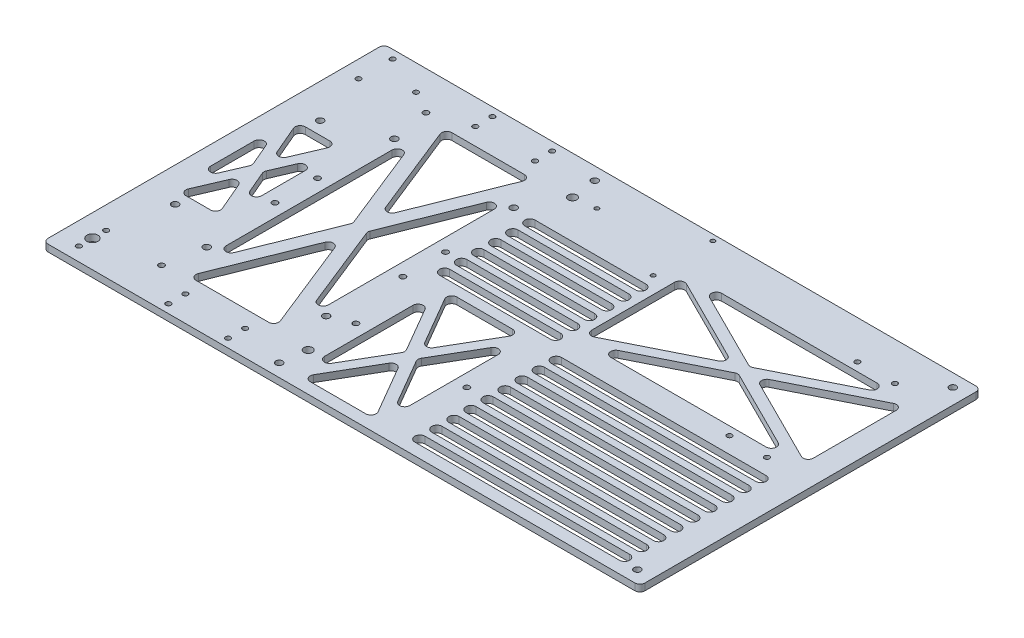
SolidWorks part; units mm, degrees
material "7075-T6 (SN)"
ref_plane "前视基准面" through (0, 0, 0) normal (0, 0, 1) x (1, 0, 0)
ref_plane "上视基准面" through (0, 0, 0) normal (0, 1, 0) x (1, 0, 0)
ref_plane "右视基准面" through (0, 0, 0) normal (1, 0, 0) x (0, 0, -1)
sketch "草图1" plane through (0, 0, 0) normal (0, 1, 0) x (1, 0, 0)
  line L1 (-114, -100) -> (114, -100)
  line L2 (-114, -100) -> (-114, 100)
  line L3 (-114, 100) -> (114, 100)
  line L4 (114, -100) -> (114, 100)
  line L5 (-114, -100) -> (114, 100) construction
  line L6 (-114, 100) -> (114, -100) construction
  point P0 (0, 0)
  dimension "D1" = 228
  dimension "D2" = 200
extrude "凸台-拉伸1" add sketch "草图1" along normal blind 4
sketch "草图2" plane through (0, 4, 0) normal (0, 1, 0) x (1, 0, 0)
  line L1 (-100, -57.5) -> (100, -57.5) construction
  line L2 (-100, -57.5) -> (-100, 57.5) construction
  line L3 (-100, 57.5) -> (100, 57.5) construction
  line L4 (100, -57.5) -> (100, 57.5) construction
  line L5 (-100, -57.5) -> (100, 57.5) construction
  line L6 (-100, 57.5) -> (100, -57.5) construction
  circle A0 centre (-100, 57.5) radius 1.5
  circle A1 centre (100, 57.5) radius 1.5
  circle A2 centre (100, -57.5) radius 1.5
  circle A3 centre (-100, -57.5) radius 1.5
  point P0 (0, 0)
  dimension "D3" = 3
  dimension "D1" = 200
  dimension "D2" = 115
sketch "草图4" plane through (0, 4, 0) normal (0, 1, 0) x (1, 0, 0)
  line L0 (0, 0) -> (-108, 0) construction
  line L1 (-108, -30) -> (-108, 30) construction
  circle A0 centre (-108, 30) radius 2.5
  circle A1 centre (-108, -30) radius 2.5
  point P6 (-108, 0)
  dimension "D2" = 5
  dimension "D1" = 108
  dimension "D3" = 60
sketch "草图5" plane through (0, 0, 0) normal (0, -1, 0) x (-1, 0, 0)
  line L1 (-10, -42) -> (-85, -42) construction
  line L2 (-10, -42) -> (-10, -20) construction
  line L3 (-10, -20) -> (-85, -20) construction
  line L4 (-85, -42) -> (-85, -20) construction
  circle A0 centre (-10, -42) radius 1.5
  circle A1 centre (-10, -20) radius 1.5
  circle A2 centre (-85, -42) radius 1.5
  circle A3 centre (-85, -20) radius 1.5
  dimension "D3" = 3
  dimension "D1" = 75
  dimension "D2" = 22
  dimension "D4" = 10
  dimension "D5" = 20
sketch "草图7" plane through (-114, 0, 0) normal (-1, 0, 0) x (0, 0, 1)
  line L4 (-100, 0) -> (100, 0)
  line L5 (100, 0) -> (100, 4)
  line L6 (100, 4) -> (-100, 4)
  line L7 (-100, 4) -> (-100, 0)
  line L8 (-100, 0) -> (100, 0)
  line L9 (100, 0) -> (100, 4)
  line L10 (100, 4) -> (-100, 4)
  line L11 (-100, 4) -> (-100, 0)
  dimension "D1" = 0
extrude "凸台-拉伸2" add sketch "草图7" along normal blind 122
sketch "草图10" plane through (0, 4, 0) normal (0, 1, 0) x (1, 0, 0)
  line L1 (-105, 92.5) -> (105, 92.5) construction
  line L2 (-105, 92.5) -> (-105, -92.5) construction
  line L3 (-105, -92.5) -> (105, -92.5) construction
  line L4 (105, 92.5) -> (105, -92.5) construction
  line L5 (-105, 92.5) -> (105, -92.5) construction
  line L6 (-105, -92.5) -> (105, 92.5) construction
  circle A0 centre (-105, 92.5) radius 2
  circle A1 centre (-105, -92.5) radius 2
  circle A2 centre (105, -92.5) radius 2
  circle A3 centre (105, 92.5) radius 2
  point P0 (0, 0)
  dimension "D3" = 4
  dimension "D1" = 185
  dimension "D2" = 210
extrude "切除-拉伸5" cut sketch "草图10" against normal through all
sketch "草图17" plane through (0, 4, 0) normal (0, 1, 0) x (1, 0, 0)
  line L0 (-236, 0) -> (-216, 0) construction
  line L2 (-216, -42.5) -> (-216, 42.5) construction
  line L4 (-236, -100) -> (-236, 100) construction
  line L5 (-236, 100) -> (-236, -100) construction
  circle A0 centre (-216, 42.5) radius 2
  circle A1 centre (-216, -42.5) radius 2
  point P8 (-216, 0)
  dimension "D3" = 4
  dimension "D1" = 85
  dimension "D2" = 20
  dimension "D4" = 0
extrude "切除-拉伸9" cut sketch "草图17" against normal through all
sketch "草图18" plane through (0, 4, 0) normal (0, 1, 0) x (1, 0, 0)
  line L0 (-236, 85) -> (-226, 85) construction
  line L1 (-236, -100) -> (-236, 100) construction
  line L2 (-226, 95) -> (-226, 75) construction
  line L3 (-226, 85) -> (-202.3, 85) construction
  line L5 (-236, 100) -> (-236, -100) construction
  line L6 (114, 100) -> (-236, 100) construction
  circle A0 centre (-226, 95) radius 1.5
  circle A1 centre (-226, 75) radius 1.5
  circle A2 centre (-202.3, 85) radius 1.5
  point P7 (-226, 85)
  dimension "D2" = 3
  dimension "D1" = 20
  dimension "D3" = 23.7
  dimension "D4" = 10
  dimension "D5" = 15
extrude "切除-拉伸11" cut sketch "草图18" against normal through all
sketch "草图19" plane through (0, 0, 0) normal (0, -1, 0) x (1, 0, 0)
  line L0 (-236, 84) -> (-223, 84) construction
  line L1 (-236, -100) -> (-236, 100) construction
  line L2 (-223, 92) -> (-223, 76) construction
  line L4 (-236, 100) -> (114, 100) construction
  circle A0 centre (-223, 92) radius 1.5
  circle A1 centre (-223, 76) radius 1.5
  circle A2 centre (-223, 84) radius 3.2
  point P6 (-223, 84)
  dimension "D4" = 3
  dimension "D5" = 6.4
  dimension "D1" = 16
  dimension "D2" = 13
  dimension "D3" = 8
extrude "切除-拉伸12" cut sketch "草图19" against normal through all
sketch "草图23" plane through (0, 0, 0) normal (0, -1, 0) x (1, 0, 0)
  line L0 (0, 0) -> (-150, 0) construction
  line L2 (-115, -55) -> (-185, -55) construction
  line L3 (-115, -55) -> (-115, 55) construction
  line L4 (-115, 55) -> (-185, 55) construction
  line L5 (-185, -55) -> (-185, 55) construction
  line L6 (-115, -55) -> (-185, 55) construction
  line L7 (-115, 55) -> (-185, -55) construction
  circle A0 centre (-185, -55) radius 2
  circle A1 centre (-115, -55) radius 2
  circle A2 centre (-185, 55) radius 2
  circle A3 centre (-115, 55) radius 2
  dimension "D4" = 4
  dimension "D1" = 110
  dimension "D2" = 70
  dimension "D3" = 150
extrude "切除-拉伸15" cut sketch "草图23" against normal through all
sketch "草图25" plane through (0, 0, 0) normal (0, -1, 0) x (1, 0, 0)
  line L0 (-70, 60) -> (0, 60) construction
  line L1 (-95, 42.5) -> (-45, 42.5) construction
  line L2 (-95, 42.5) -> (-95, 77.5) construction
  line L3 (-95, 77.5) -> (-45, 77.5) construction
  line L4 (-45, 42.5) -> (-45, 77.5) construction
  line L5 (-95, 42.5) -> (-45, 77.5) construction
  line L6 (-95, 77.5) -> (-45, 42.5) construction
  line L7 (0, 0) -> (0, 60) construction
  circle A3 centre (-45, 77.5) radius 1.5
  circle A4 centre (-45, 42.5) radius 1.5
  circle A5 centre (-95, 60) radius 1.5
  point P0 (-70, 60)
  dimension "D4" = 3
  dimension "D1" = 70
  dimension "D2" = 35
  dimension "D3" = 50
  dimension "D5" = 60
hole_wizard "M3 螺纹孔2" [suppressed] positions "3D草图2" profile "草图27" tap size "M3" standard "ISO"
sketch3d "3D草图2"
  point P0 (-95, 0, 60)
  point P3 (-45, 0, 77.5)
  point P6 (-45, 0, 42.5)
sketch "草图27" plane through (-95, 0, 60) normal (1, 0, 0) x (0, 0, -1)
  line L0 (0, 0) -> (0, 3)
  line L1 (0, 3) -> (1.25, 3)
  line L2 (1.25, 3) -> (1.25, 0)
  line L5 (1.25, 0) -> (0, 0)
  line L11 (0, -6.35) -> (0, 107.95) construction
  dimension "通孔螺纹孔钻头直径" = 2.5
  dimension "通孔螺纹孔钻头深度" = 3
cosmetic thread "孔螺蚊线4" [suppressed] parameters "D2"=3
cosmetic thread "孔螺蚊线5" [suppressed] parameters "D2"=3
cosmetic thread "孔螺蚊线6" [suppressed] parameters "D2"=3
sketch "草图28" plane through (0, 0, 0) normal (0, -1, 0) x (1, 0, 0)
  line L0 (-60, 0) -> (0, 0) construction
  line L2 (-115, -35) -> (-5, -35) construction
  line L3 (-115, -35) -> (-115, 35) construction
  line L4 (-115, 35) -> (-5, 35) construction
  line L5 (-5, -35) -> (-5, 35) construction
  line L6 (-115, -35) -> (-5, 35) construction
  line L7 (-115, 35) -> (-5, -35) construction
  circle A0 centre (-115, 35) radius 2
  circle A1 centre (-5, 35) radius 2
  circle A2 centre (-115, -35) radius 2
  circle A3 centre (-5, -35) radius 2
  dimension "D4" = 4
  dimension "D1" = 60
  dimension "D2" = 110
  dimension "D3" = 70
extrude "切除-拉伸16" [suppressed] cut sketch "草图28" against normal through all
sketch "草图29" [suppressed] plane through (0, 0, 0) normal (0, -1, 0) x (-1, 0, 0)
  line L0 (115, -35) -> (5, 35) construction
  line L1 (92.5, 0) -> (27.5, 0) construction
  circle A0 centre (92.5, 0) radius 2
  circle A1 centre (27.5, 0) radius 2
  point P8 (60, 0)
  dimension "D2" = 4
  dimension "D1" = 65
extrude "切除-拉伸17" [suppressed] cut sketch "草图29" against normal through all
sketch "草图30" plane through (0, 0, 0) normal (0, -1, 0) x (1, 0, 0)
  line L1 (86, -2.5) -> (64, -2.5) construction
  line L2 (86, -2.5) -> (86, -77.5) construction
  line L3 (86, -77.5) -> (64, -77.5) construction
  line L4 (64, -2.5) -> (64, -77.5) construction
  line L5 (86, -2.5) -> (64, -77.5) construction
  line L6 (86, -77.5) -> (64, -2.5) construction
  circle A0 centre (86, -77.5) radius 1.5
  circle A1 centre (64, -77.5) radius 1.5
  circle A2 centre (64, -2.5) radius 1.5
  circle A3 centre (86, -2.5) radius 1.5
  point P0 (75, -40)
  dimension "D5" = 3
  dimension "D1" = 75
  dimension "D2" = 22
  dimension "D3" = 75
  dimension "D4" = 40
extrude "切除-拉伸18" cut sketch "草图30" against normal through all
sketch "草图33" plane through (0, 4, 0) normal (0, 1, 0) x (1, 0, 0)
  line L0 (-236, 77.5) -> (-189, 77.5) construction
  line L1 (-236, -100) -> (-236, 100) construction
  line L2 (-189, 77.5) -> (-189, 100) construction
  line L3 (114, 100) -> (-236, 100) construction
  dimension "D1" = 47
  dimension "D2" = 22.5
hole_wizard "M4 螺纹孔3" positions "3D草图3" profile "草图34" tap size "M4" standard "ISO" end condition up to next
sketch3d "3D草图3"
  point P0 (-189, 4, -77.5)
sketch "草图34" plane through (-189, 4, -77.5) normal (1, 0, 0) x (0, 0, 1)
  line L0 (0, 0) -> (0, 4)
  line L1 (0, 4) -> (1.65, 4)
  line L2 (1.65, 4) -> (1.65, 0)
  line L5 (1.65, 0) -> (0, 0)
  line L11 (0, -6.35) -> (0, 107.95) construction
  dimension "通孔螺纹孔钻头直径" = 3.3
  dimension "通孔螺纹孔钻头深度" = 4
cosmetic thread "孔螺蚊线7" parameters "D2"=4
mirror "镜向1" about plane through (0, 0, 0) normal (0, 0, 1) of "M4 螺纹孔3"
cosmetic thread "孔螺蚊线8" parameters "D2"=4
sketch "草图35" plane through (0, 0, 0) normal (0, -1, 0) x (1, 0, 0)
  line L0 (-150, 0) -> (0, 0) construction
  line L1 (-167.5, 95) -> (-132.5, 95) construction
  line L2 (-167.5, 95) -> (-167.5, -95) construction
  line L3 (-167.5, -95) -> (-132.5, -95) construction
  line L4 (-132.5, 95) -> (-132.5, -95) construction
  line L5 (-167.5, 95) -> (-132.5, -95) construction
  line L6 (-167.5, -95) -> (-132.5, 95) construction
  line L8 (-167.5, 85) -> (-132.5, 85) construction
  line L9 (-167.5, 85) -> (-167.5, -85) construction
  line L10 (-167.5, -85) -> (-132.5, -85) construction
  line L11 (-132.5, 85) -> (-132.5, -85) construction
  line L12 (-167.5, 85) -> (-132.5, -85) construction
  line L13 (-167.5, -85) -> (-132.5, 85) construction
  circle A0 centre (-167.5, 95) radius 1.5
  circle A1 centre (-132.5, 95) radius 1.5
  circle A2 centre (-167.5, -95) radius 1.5
  circle A3 centre (-132.5, -95) radius 1.5
  circle A4 centre (-132.5, 85) radius 1.5
  circle A5 centre (-167.5, 85) radius 1.5
  circle A6 centre (-132.5, -85) radius 1.5
  circle A7 centre (-167.5, -85) radius 1.5
  point P0 (-150, 0)
  dimension "D4" = 3
  dimension "D1" = 150
  dimension "D2" = 190
  dimension "D3" = 35
  dimension "D5" = 10
extrude "切除-拉伸19" cut sketch "草图35" against normal through all
sketch "草图37" plane through (0, 0, 0) normal (0, -1, 0) x (-1, 0, 0)
  line L0 (150, 0) -> (0, 0) construction
  line L1 (187.5, 12.5) -> (112.5, 12.5) construction
  line L2 (187.5, 12.5) -> (187.5, -12.5) construction
  line L3 (187.5, -12.5) -> (112.5, -12.5) construction
  line L4 (112.5, 12.5) -> (112.5, -12.5) construction
  line L5 (187.5, 12.5) -> (112.5, -12.5) construction
  line L6 (187.5, -12.5) -> (112.5, 12.5) construction
  point P0 (150, 0)
  dimension "D1" = 25
  dimension "D2" = 75
  dimension "D3" = 150
hole_wizard "M4 螺纹孔1" positions "3D草图4" profile "草图38" tap size "M4" standard "ISO" end condition up to next
sketch3d "3D草图4"
  point P0 (-112.5, 0, -12.5)
  point P3 (-112.5, 0, 12.5)
  point P6 (-187.5, 0, 12.5)
  point P9 (-187.5, 0, -12.5)
sketch "草图38" plane through (-112.5, 0, -12.5) normal (1, 0, 0) x (0, 0, -1)
  line L0 (0, 0) -> (0, 4)
  line L1 (0, 4) -> (1.65, 4)
  line L2 (1.65, 4) -> (1.65, 0)
  line L5 (1.65, 0) -> (0, 0)
  line L11 (0, -6.35) -> (0, 107.95) construction
  dimension "通孔螺纹孔钻头直径" = 3.3
  dimension "通孔螺纹孔钻头深度" = 4
cosmetic thread "孔螺蚊线9" parameters "D2"=4
cosmetic thread "孔螺蚊线10" parameters "D2"=4
cosmetic thread "孔螺蚊线11" parameters "D2"=4
cosmetic thread "孔螺蚊线12" parameters "D2"=4
sketch "草图39" plane through (0, 0, 0) normal (0, -1, 0) x (-1, 0, 0)
  line L0 (0, 0) -> (-75, 0) construction
  line L1 (-75, 0) -> (-75, -20) construction
  line L2 (-86, 77.5) -> (-64, 77.5) construction
  line L3 (-75, 77.5) -> (-75, 0) construction
  line L4 (-25.5676, -57.7053) -> (-120.5676, 22.2947)
  line L5 (-27.5, -60) -> (-122.5, -60)
  line L6 (-27.5, -60) -> (-27.5, 20)
  line L7 (-27.5, 20) -> (-122.5, 20)
  line L8 (-122.5, -60) -> (-122.5, 20)
  line L9 (-27.5, -60) -> (-122.5, 20) construction
  line L10 (-27.5, 20) -> (-122.5, -60) construction
  line L11 (-29.4324, 22.2947) -> (-124.4324, -57.7053)
  line L12 (-29.4324, -62.2947) -> (-124.4324, 17.7053)
  line L13 (-25.5676, 17.7053) -> (-120.5676, -62.2947)
  dimension "D1" = 20
  dimension "D2" = 80
  dimension "D3" = 95
  dimension "D4" = 3
  dimension "D5" = 3
extrude "切除-拉伸20" [suppressed] cut sketch "草图39" against normal blind 10 contours L12 L13 L5 | L6 L13 L4 | L11 L7 L4 | L11 L12 L8
sketch "草图40" plane through (0, 0, 0) normal (0, -1, 0) x (-1, 0, 0)
  line L0 (0, 0) -> (-50, 0) construction
  line L1 (-10, -60) -> (-90, -60)
  line L2 (-10, -60) -> (-10, -10)
  line L3 (-10, -10) -> (-90, -10)
  line L4 (-90, -60) -> (-90, -10)
  line L5 (-10, -60) -> (-90, -10) construction
  line L6 (-10, -10) -> (-90, -60) construction
  line L7 (-50, 0) -> (-50, -35) construction
  line L8 (236, -100) -> (-114, -100) construction
  line L9 (-8.41, -57.456) -> (-88.41, -7.456)
  line L10 (-11.59, -7.456) -> (-91.59, -57.456)
  line L11 (-11.59, -62.544) -> (-91.59, -12.544)
  line L12 (-8.41, -12.544) -> (-88.41, -62.544)
  point P0 (-50, -35)
  dimension "D1" = 50
  dimension "D2" = 80
  dimension "D3" = 50
  dimension "D4" = 40
  dimension "D5" = 3
  dimension "D6" = 3
extrude "切除-拉伸21" [suppressed] cut sketch "草图40" against normal blind 10 contours L2 L12 L9 | L11 L12 L1 | L10 L11 L4 | L10 L3 L9
mirror "镜向2" [suppressed] about plane through (0, 0, 0) normal (0, 0, 1)
sketch "草图43" plane through (0, 0, 0) normal (0, -1, 0) x (-1, 0, 0)
  line L0 (185, -55) -> (115, 55) construction
  line L1 (183.7139, -73.5144) -> (123.7139, 76.4856)
  line L2 (180, 75) -> (120, 75)
  line L3 (180, 75) -> (180, -75)
  line L4 (180, -75) -> (120, -75)
  line L5 (120, 75) -> (120, -75)
  line L6 (180, 75) -> (120, -75) construction
  line L7 (180, -75) -> (120, 75) construction
  line L8 (176.2861, 76.4856) -> (116.2861, -73.5144)
  line L9 (176.2861, -76.4856) -> (116.2861, 73.5144)
  line L10 (183.7139, 73.5144) -> (123.7139, -76.4856)
  point P4 (150, 0)
  dimension "D1" = 60
  dimension "D2" = 150
  dimension "D3" = 4
  dimension "D4" = 4
extrude "切除-拉伸22" cut sketch "草图43" against normal blind 10 contours L9 L10 L4 | L8 L9 L5 | L8 L2 L1 | L3 L10 L1
fillet "圆角1" [suppressed] radius 3
sketch "草图44" [suppressed] plane through (0, 0, 0) normal (0, -1, 0) x (1, 0, 0)
  line L0 (-97.5, -29) -> (-22.5, -51) construction
  line L1 (-60, -40) -> (-60, -58) construction
  line L2 (-102.8426, -20) -> (-17.1574, -20) construction
  line L3 (-35, -88) -> (-85, -88)
  line L4 (-35, -88) -> (-35, -28)
  line L5 (-35, -28) -> (-85, -28)
  line L6 (-85, -88) -> (-85, -28)
  line L7 (-35, -88) -> (-85, -28) construction
  line L8 (-35, -28) -> (-85, -88) construction
  line L10 (-32.6953, -86.0794) -> (-82.6953, -26.0794)
  line L11 (-37.3047, -26.0794) -> (-87.3047, -86.0794)
  line L12 (-37.3047, -89.9206) -> (-87.3047, -29.9206)
  line L13 (-32.6953, -29.9206) -> (-82.6953, -89.9206)
  dimension "D1" = 50
  dimension "D2" = 60
  dimension "D3" = 8
  dimension "D4" = 3
  dimension "D5" = 3
extrude "切除-拉伸23" [suppressed] cut sketch "草图44" against normal blind 10 contours L11 L5 L10 | L4 L13 L10 | L12 L13 L3 | L11 L12 L6
sketch "草图45" plane through (0, 0, 0) normal (0, -1, 0) x (1, 0, 0)
  line L0 (0, 0) -> (-70, 0) construction
  line L1 (-70, 50) -> (-70, 0) construction
  line L2 (-37.5, 50) -> (-102.5, 50) construction
  circle A0 centre (-37.5, 50) radius 2
  circle A1 centre (-102.5, 50) radius 2
  point P6 (-70, 50)
  dimension "D4" = 4
  dimension "D1" = 65
  dimension "D2" = 50
  dimension "D3" = 70
hole_wizard "M4 螺纹孔2" positions "3D草图6" profile "草图47" tap size "M4" standard "ISO" end condition up to next
sketch3d "3D草图6"
  point P0 (-37.5, 0, 50)
  point P3 (-102.5, 0, 50)
sketch "草图47" plane through (-37.5, 0, 50) normal (1, 0, 0) x (0, 0, -1)
  line L0 (0, 0) -> (0, 4)
  line L1 (0, 4) -> (1.65, 4)
  line L2 (1.65, 4) -> (1.65, 0)
  line L5 (1.65, 0) -> (0, 0)
  line L11 (0, -6.35) -> (0, 107.95) construction
  dimension "通孔螺纹孔钻头直径" = 3.3
  dimension "通孔螺纹孔钻头深度" = 4
cosmetic thread "孔螺蚊线13" parameters "D2"=4
cosmetic thread "孔螺蚊线14" parameters "D2"=4
sketch "草图48" plane through (0, 0, 0) normal (0, -1, 0) x (1, 0, 0)
  line L0 (0, 0) -> (-65, 0) construction
  line L1 (-65, 0) -> (-65, -79) construction
  line L2 (-65, -79) -> (-90.25, -79) construction
  line L3 (-90.25, -61.5) -> (-39.75, -61.5) construction
  line L4 (-90.25, -61.5) -> (-90.25, -96.5) construction
  line L5 (-90.25, -96.5) -> (-39.75, -96.5) construction
  line L6 (-39.75, -61.5) -> (-39.75, -96.5) construction
  line L7 (-90.25, -61.5) -> (-39.75, -96.5) construction
  line L8 (-90.25, -96.5) -> (-39.75, -61.5) construction
  circle A0 centre (-39.75, -61.5) radius 1.5
  circle A1 centre (-39.75, -96.5) radius 1.5
  circle A2 centre (-90.25, -79) radius 1.5
  dimension "D5" = 3
  dimension "D1" = 50.5
  dimension "D2" = 35
  dimension "D3" = 65
  dimension "D4" = 79
hole_wizard "M3 螺纹孔4" positions "3D草图7" profile "草图49" tap size "M3" standard "ISO" end condition up to next
sketch3d "3D草图7"
  point P0 (-90.25, 0, -79)
  point P3 (-39.75, 0, -61.5)
  point P6 (-39.75, 0, -96.5)
sketch "草图49" plane through (-90.25, 0, -79) normal (1, 0, 0) x (0, 0, -1)
  line L0 (0, 0) -> (0, 4)
  line L1 (0, 4) -> (1.25, 4)
  line L2 (1.25, 4) -> (1.25, 0)
  line L5 (1.25, 0) -> (0, 0)
  line L11 (0, -6.35) -> (0, 107.95) construction
  dimension "通孔螺纹孔钻头直径" = 2.5
  dimension "通孔螺纹孔钻头深度" = 4
cosmetic thread "孔螺蚊线15" parameters "D2"=3
cosmetic thread "孔螺蚊线16" parameters "D2"=3
cosmetic thread "孔螺蚊线17" parameters "D2"=3
sketch "草图51" plane through (0, 0, 0) normal (0, -1, 0) x (-1, 0, 0)
  line L0 (0, 0) -> (-35, 0) construction
  line L1 (-35, 0) -> (-35, -30) construction
  line L6 (236, -100) -> (-114, -100) construction
  line L11 (30, -80) -> (-100, -80)
  line L12 (30, -80) -> (30, 20)
  line L13 (30, 20) -> (-100, 20)
  line L14 (-100, -80) -> (-100, 20)
  line L15 (30, -80) -> (-100, 20) construction
  line L16 (30, 20) -> (-100, -80) construction
  line L17 (31.8291, -77.6221) -> (-98.1709, 22.3779)
  line L18 (28.1709, 22.3779) -> (-101.8291, -77.6221)
  line L19 (28.1709, -82.3779) -> (-101.8291, 17.6221)
  line L20 (31.8291, 17.6221) -> (-98.1709, -82.3779)
  dimension "D1" = 130
  dimension "D2" = 100
  dimension "D3" = 20
  dimension "D4" = 35
  dimension "D5" = 3
  dimension "D6" = 3
extrude "切除-拉伸25" [suppressed] cut sketch "草图51" against normal blind 10 contours L19 L20 L11 | L18 L19 L14 | L18 L13 L17 | L12 L20 L17
sketch "草图52" plane through (0, 0, 0) normal (0, -1, 0) x (1, 0, 0)
  line L0 (-39.75, -61.5) -> (-39.75, -96.5) construction
  line L1 (-90.25, -79) -> (-39.75, -79) construction
  line L2 (-236, 100) -> (114, 100) construction
  line L3 (-80, -238) -> (-50, -238)
  line L4 (-80, -238) -> (-80, 80)
  line L5 (-80, 80) -> (-50, 80)
  line L6 (-50, -238) -> (-50, 80)
  line L7 (-80, -238) -> (-50, 80) construction
  line L8 (-80, 80) -> (-50, -238) construction
  line L9 (-82.9867, 79.7182) -> (-52.9867, -238.2818)
  line L10 (-77.0133, -238.2818) -> (-47.0133, 79.7182)
  line L11 (-77.0133, 80.2818) -> (-47.0133, -237.7182)
  line L12 (-82.9867, -237.7182) -> (-52.9867, 80.2818)
  point P7 (-65, -79)
  point P14 (-65, -79)
  dimension "D1" = 20
  dimension "D2" = 30
  dimension "D3" = 3
  dimension "D4" = 3
extrude "切除-拉伸26" [suppressed] cut sketch "草图52" against normal blind 10 contours L11 L12 L5 | L10 L11 L6 | L10 L3 L9 | L4 L12 L9
sketch "草图53" plane through (0, 0, 0) normal (0, -1, 0) x (-1, 0, 0)
  line L0 (-64, 2.5) -> (-86, 77.5) construction
  line L1 (-75, 40) -> (-75, 60) construction
  line L2 (-47.6953, 31.9206) -> (-97.6953, 91.9206)
  line L3 (-50, 30) -> (-100, 30)
  line L4 (-50, 30) -> (-50, 90)
  line L5 (-50, 90) -> (-100, 90)
  line L6 (-100, 30) -> (-100, 90)
  line L7 (-50, 30) -> (-100, 90) construction
  line L8 (-50, 90) -> (-100, 30) construction
  line L9 (-52.3047, 91.9206) -> (-102.3047, 31.9206)
  line L10 (-52.3047, 28.0794) -> (-102.3047, 88.0794)
  line L11 (-47.6953, 88.0794) -> (-97.6953, 28.0794)
  dimension "D1" = 50
  dimension "D2" = 60
  dimension "D3" = 20
  dimension "D4" = 3
  dimension "D5" = 3
extrude "切除-拉伸27" [suppressed] cut sketch "草图53" against normal blind 10 contours L9 L5 L2 | L4 L11 L2 | L10 L11 L3 | L9 L10 L6
sketch "草图54" plane through (114, 0, 0) normal (1, 0, 0) x (0, 0, -1)
  line L4 (-100, 0) -> (100, 0)
  line L5 (100, 0) -> (100, 4)
  line L6 (100, 4) -> (-100, 4)
  line L7 (-100, 4) -> (-100, 0)
  line L8 (-100, 0) -> (100, 0)
  line L9 (100, 0) -> (100, 4)
  line L10 (100, 4) -> (-100, 4)
  line L11 (-100, 4) -> (-100, 0)
  dimension "D1" = 0
extrude "凸台-拉伸3" [suppressed] add sketch "草图54" along normal blind 10
sketch "草图56" [suppressed] plane through (0, 3, 0) normal (0, 1, 0) x (1, 0, 0)
  line L0 (0, 0) -> (119, 0) construction
  line L1 (119, 40) -> (119, -40) construction
  line L2 (124, 100) -> (124, -100) construction
  circle A0 centre (119, 40) radius 2.5
  circle A1 centre (119, -40) radius 2.5
  point P6 (119, 0)
  dimension "D3" = 5
  dimension "D1" = 5
  dimension "D2" = 80
extrude "切除-拉伸28" [suppressed] cut sketch "草图56" against normal through all
sketch "草图57" plane through (0, 0, 0) normal (0, -1, 0) x (-1, 0, 0)
  line L0 (39.75, 96.5) -> (39.75, 61.5) construction
  line L1 (90.25, 79) -> (39.75, 79) construction
  line L3 (40, 106.5) -> (90, 106.5) construction
  line L4 (40, 106.5) -> (40, 51.5) construction
  line L5 (40, 51.5) -> (90, 51.5) construction
  line L6 (90, 106.5) -> (90, 51.5) construction
  line L7 (40, 106.5) -> (90, 51.5) construction
  line L8 (40, 51.5) -> (90, 106.5) construction
  circle A0 centre (40, 106.5) radius 1.65
  circle A1 centre (90, 106.5) radius 1.65
  circle A2 centre (90, 51.5) radius 1.65
  circle A3 centre (40, 51.5) radius 1.65
  point P7 (65, 79)
  dimension "D3" = 3.3
  dimension "D1" = 55
  dimension "D2" = 50
extrude "切除-拉伸29" [suppressed] cut sketch "草图57" against normal blind 10
sketch "草图58" plane through (0, 0, 0) normal (0, -1, 0) x (-1, 0, 0)
  line L1 (-114, -100) -> (103, -100) construction
  line L2 (-114, -100) -> (-114, -77.5) construction
  line L3 (-114, -77.5) -> (103, -77.5) construction
  line L4 (103, -100) -> (103, -77.5) construction
  circle A0 centre (103, -77.5) radius 2.5
  dimension "D3" = 5
  dimension "D1" = 22.5
  dimension "D2" = 217
extrude "切除-拉伸30" cut sketch "草图58" against normal through all
mirror "镜向3" about plane through (0, 0, 0) normal (0, 0, 1) of "切除-拉伸30"
sketch "草图59" plane through (0, 0, 0) normal (0, -1, 0) x (1, 0, 0)
  line L0 (0, 0) -> (35, 0) construction
  line L1 (35, 0) -> (35, 90) construction
  line L2 (-25, 90) -> (95, 90) construction
  line L3 (-25, 93) -> (95, 93)
  line L4 (-25, 87) -> (95, 87)
  arc A0 (-25, 93) -> (-25, 87) centre (-25, 90) ccw
  arc A1 (95, 87) -> (95, 93) centre (95, 90) ccw
  point P6 (35, 90)
  dimension "D2" = 3
  dimension "D1" = 120
  dimension "D3" = 35
  dimension "D4" = 90
extrude "切除-拉伸31" cut sketch "草图59" against normal through all
pattern_linear "阵列(线性)1" count 9 spacing 10 along (0, 0, -1) of "切除-拉伸31"
sketch "草图60" plane through (0, 0, 0) normal (0, -1, 0) x (-1, 0, 0)
  line L0 (-86, 2.5) -> (-64, 77.5) construction
  line L1 (-75, 40) -> (-35, 40) construction
  line L2 (31.3416, 10.1833) -> (-98.6584, 75.1833)
  line L3 (30, 72.5) -> (-100, 72.5)
  line L4 (30, 72.5) -> (30, 7.5)
  line L5 (30, 7.5) -> (-100, 7.5)
  line L6 (-100, 72.5) -> (-100, 7.5)
  line L7 (30, 72.5) -> (-100, 7.5) construction
  line L8 (30, 7.5) -> (-100, 72.5) construction
  line L9 (28.6584, 75.1833) -> (-101.3416, 10.1833)
  line L10 (28.6584, 4.8167) -> (-101.3416, 69.8167)
  line L11 (31.3416, 69.8167) -> (-98.6584, 4.8167)
  dimension "D1" = 35
  dimension "D2" = 130
  dimension "D3" = 65
  dimension "D4" = 3
  dimension "D5" = 3
extrude "切除-拉伸32" cut sketch "草图60" against normal blind 10 contours L10 L11 L5 | L4 L11 L2 | L9 L3 L2 | L9 L10 L6
sketch "草图62" plane through (0, 0, 0) normal (0, -1, 0) x (-1, 0, 0)
  line L0 (102.5, -50) -> (37.5, -50) construction
  line L1 (-95, -93) -> (25, -93) construction
  line L2 (95, -93) -> (45, -93)
  line L3 (95, -93) -> (95, -7)
  line L4 (95, -7) -> (45, -7)
  line L5 (45, -93) -> (45, -7)
  line L6 (95, -93) -> (45, -7) construction
  line L7 (95, -7) -> (45, -93) construction
  line L8 (97.5935, -91.4921) -> (47.5935, -5.4921)
  line L9 (92.4065, -5.4921) -> (42.4065, -91.4921)
  line L10 (92.4065, -94.5079) -> (42.4065, -8.5079)
  line L11 (97.5935, -8.5079) -> (47.5935, -94.5079)
  point P4 (70, -50)
  dimension "D1" = 50
  dimension "D2" = 3
  dimension "D3" = 3
extrude "切除-拉伸33" cut sketch "草图62" against normal blind 10 contours L10 L11 L2 | L3 L11 L8 | L9 L10 L5 | L9 L4 L8
sketch "草图63" plane through (0, 0, 0) normal (0, -1, 0) x (-1, 0, 0)
  line L0 (70, -7) -> (70, -1) construction
  line L1 (91.5298, -7) -> (48.4702, -7) construction
  line L2 (70, -1) -> (70, 2) construction
  line L4 (102.5, 2) -> (37.5, 2) construction
  line L5 (102.5, -1) -> (37.5, -1)
  line L6 (102.5, 5) -> (37.5, 5)
  arc A0 (102.5, -1) -> (102.5, 5) centre (102.5, 2) ccw
  arc A1 (37.5, 5) -> (37.5, -1) centre (37.5, 2) ccw
  point P8 (70, 2)
  dimension "D2" = 3
  dimension "D1" = 3
  dimension "D3" = 65
  dimension "D4" = 6
extrude "切除-拉伸34" cut sketch "草图63" against normal through all
pattern_linear "阵列(线性)2" count 6 spacing 10 along (0, 0, -1) of "切除-拉伸34"
sketch "草图65" plane through (0, 0, 0) normal (0, -1, 0) x (-1, 0, 0)
  line L0 (0, 0) -> (210, 0) construction
  line L1 (227.7574, -33.8182) -> (197.7574, 36.1818)
  line L2 (225, 35) -> (195, 35)
  line L3 (225, 35) -> (225, -35)
  line L4 (225, -35) -> (195, -35)
  line L5 (195, 35) -> (195, -35)
  line L6 (225, 35) -> (195, -35) construction
  line L7 (225, -35) -> (195, 35) construction
  line L8 (222.2426, 36.1818) -> (192.2426, -33.8182)
  line L9 (222.2426, -36.1818) -> (192.2426, 33.8182)
  line L10 (227.7574, 33.8182) -> (197.7574, -36.1818)
  dimension "D1" = 210
  dimension "D2" = 30
  dimension "D3" = 70
  dimension "D4" = 3
  dimension "D5" = 3
extrude "切除-拉伸35" cut sketch "草图65" against normal blind 10 contours L9 L10 L4 | L8 L9 L5 | L8 L2 L1 | L3 L10 L1
fillet "圆角2" radius 3 4 edges at (114, 2, 100) (114, 2, -100) (-236, 2, -100) (-236, 2, 100)
fillet "圆角3" radius 3 12 edges at (-198.2639, 2, -35) (-221.7361, 2, -35) (-210, 2, -7.6158) (-195, 2, -27.3842) (-206.7361, 2, 0) (-195, 2, 27.3842) (-213.2639, 2, 0) (-225, 2, 27.3842) (-225, 2, -27.3842) (-198.2639, 2, 35) (-210, 2, 7.6158) (-221.7361, 2, 35)
fillet "圆角4" radius 3 12 edges at (-180, 2, 64.2297) (-154.3081, 2, 0) (-180, 2, -64.2297) (-124.3081, 2, -75) (-175.6919, 2, -75) (-150, 2, -10.7703) (-120, 2, -64.2297) (-145.6919, 2, 0) (-120, 2, 64.2297) (-150, 2, 10.7703) (-124.3081, 2, 75) (-175.6919, 2, 75)
fillet "圆角5" radius 3 12 edges at (-45, 2, 87.0313) (-66.5298, 2, 50) (-45, 2, 12.9687) (-48.4702, 2, 7) (-70, 2, 44.0313) (-91.5298, 2, 7) (-95, 2, 12.9687) (-73.4702, 2, 50) (-95, 2, 87.0313) (-70, 2, 55.9687) (-48.4702, 2, 93) (-91.5298, 2, 93)
fillet "圆角6" radius 3 12 edges at (100, 2, -10.8541) (41.7082, 2, -40) (100, 2, -69.1459) (93.2918, 2, -72.5) (-23.2918, 2, -72.5) (35, 2, -43.3541) (28.2918, 2, -40) (-30, 2, -69.1459) (-30, 2, -10.8541) (93.2918, 2, -7.5) (35, 2, -36.6459) (-23.2918, 2, -7.5)
